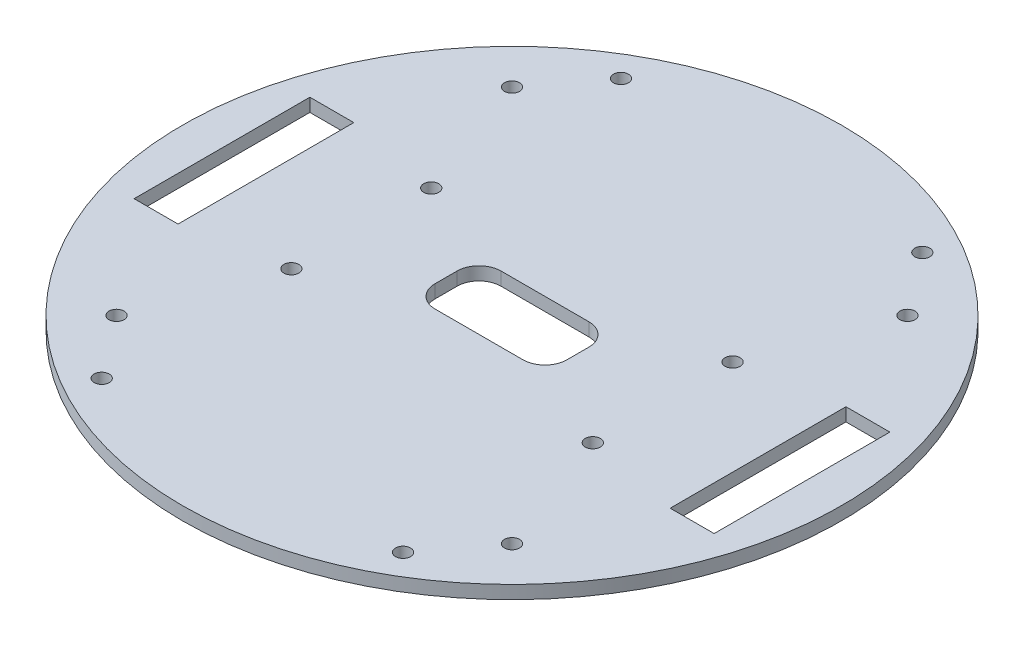
SolidWorks part; units mm, degrees
ref_plane "Front" through (0, 0, 0) normal (0, 0, 1) x (1, 0, 0)
ref_plane "Top" through (0, 0, 0) normal (0, 1, 0) x (1, 0, 0)
ref_plane "Right" through (0, 0, 0) normal (1, 0, 0) x (0, 0, -1)
sketch "Sketch1" plane through (0, 0, 0) normal (0, 1, 0) x (1, 0, 0)
  circle A0 centre (0, 0) radius 75
  dimension "D1" = 150
extrude "Boss-Extrude1" add sketch "Sketch1" along normal blind 3
sketch "Sketch2" plane through (0, 3, 0) normal (0, 1, 0) x (1, 0, 0)
  line L0 (-75, 0) -> (75, 0) construction
  line L2 (-66, -20) -> (-56, -20)
  line L3 (-66, -20) -> (-66, 20)
  line L4 (-66, 20) -> (-56, 20)
  line L5 (-56, -20) -> (-56, 20)
  line L6 (-66, -20) -> (-56, 20) construction
  line L7 (-66, 20) -> (-56, -20) construction
  line L8 (56, -20) -> (66, -20)
  line L9 (56, -20) -> (56, 20)
  line L10 (56, 20) -> (66, 20)
  line L11 (66, -20) -> (66, 20)
  line L12 (56, -20) -> (66, 20) construction
  line L13 (56, 20) -> (66, -20) construction
  circle A0 centre (0, 0) radius 75 construction
  point P5 (-61, 0)
  point P10 (61, 0)
  dimension "D1" = 40
  dimension "D2" = 40
  dimension "D3" = 10
  dimension "D4" = 10
  dimension "D5" = 61
  dimension "D6" = 61
extrude "Cut-Extrude1" cut sketch "Sketch2" against normal blind 6.35
sketch "Sketch8" plane through (0, 3, 0) normal (0, 1, 0) x (1, 0, 0)
  line L1 (45, -45) -> (-45, -45) construction
  line L2 (45, -45) -> (45, 45) construction
  line L3 (45, 45) -> (-45, 45) construction
  line L4 (-45, -45) -> (-45, 45) construction
  line L5 (45, -45) -> (-45, 45) construction
  line L6 (45, 45) -> (-45, -45) construction
  circle A0 centre (-45, 45) radius 1.7145
  circle A1 centre (45, 45) radius 1.7145
  circle A2 centre (45, -45) radius 1.7145
  circle A3 centre (-45, -45) radius 1.7145
  point P0 (0, 0)
  dimension "D3" = 3.429
  dimension "D1" = 90
  dimension "D2" = 90
extrude "Cut-Extrude7" cut sketch "Sketch8" against normal through all
sketch "Sketch9" plane through (0, 3, 0) normal (0, 1, 0) x (1, 0, 0)
  line L1 (-15, -7.5) -> (15, -7.5)
  line L2 (-15, -7.5) -> (-15, 7.5)
  line L3 (-15, 7.5) -> (15, 7.5)
  line L4 (15, -7.5) -> (15, 7.5)
  line L5 (-15, -7.5) -> (15, 7.5) construction
  line L6 (-15, 7.5) -> (15, -7.5) construction
  point P0 (0, 0)
  dimension "D1" = 30
  dimension "D2" = 15
extrude "Cut-Extrude8" cut sketch "Sketch9" against normal through all
fillet "Fillet1" radius 5 4 edges at (-15, 1.5, 7.5) (15, 1.5, 7.5) (15, 1.5, -7.5) (-15, 1.5, -7.5)
sketch "Sketch10" plane through (0, 3, 0) normal (0, 1, 0) x (1, 0, 0)
  line L1 (-34.29, -15.91) -> (34.29, -15.91) construction
  line L2 (-34.29, -15.91) -> (-34.29, -59.09) construction
  line L3 (-34.29, -59.09) -> (34.29, -59.09) construction
  line L4 (34.29, -15.91) -> (34.29, -59.09) construction
  line L5 (-34.29, -15.91) -> (34.29, -59.09) construction
  line L6 (-34.29, -59.09) -> (34.29, -15.91) construction
  line L7 (-34.29, 59.09) -> (34.29, 59.09) construction
  line L8 (-34.29, 59.09) -> (-34.29, 15.91) construction
  line L9 (-34.29, 15.91) -> (34.29, 15.91) construction
  line L10 (34.29, 59.09) -> (34.29, 15.91) construction
  line L11 (-34.29, 59.09) -> (34.29, 15.91) construction
  line L12 (-34.29, 15.91) -> (34.29, 59.09) construction
  circle A0 centre (34.29, 59.09) radius 1.7145
  circle A1 centre (34.29, 15.91) radius 1.7145
  circle A2 centre (-34.29, 15.91) radius 1.7145
  circle A3 centre (-34.29, 59.09) radius 1.7145
  circle A4 centre (-34.29, -15.91) radius 1.7145
  circle A5 centre (-34.29, -59.09) radius 1.7145
  circle A6 centre (34.29, -59.09) radius 1.7145
  circle A7 centre (34.29, -15.91) radius 1.7145
  point P0 (0, -37.5)
  point P5 (0, 37.5)
  dimension "D7" = 3.429
  dimension "D1" = 68.58
  dimension "D2" = 43.18
  dimension "D3" = 68.58
  dimension "D4" = 43.18
  dimension "D5" = 37.5
  dimension "D6" = 37.5
extrude "Cut-Extrude9" cut sketch "Sketch10" against normal blind 10
